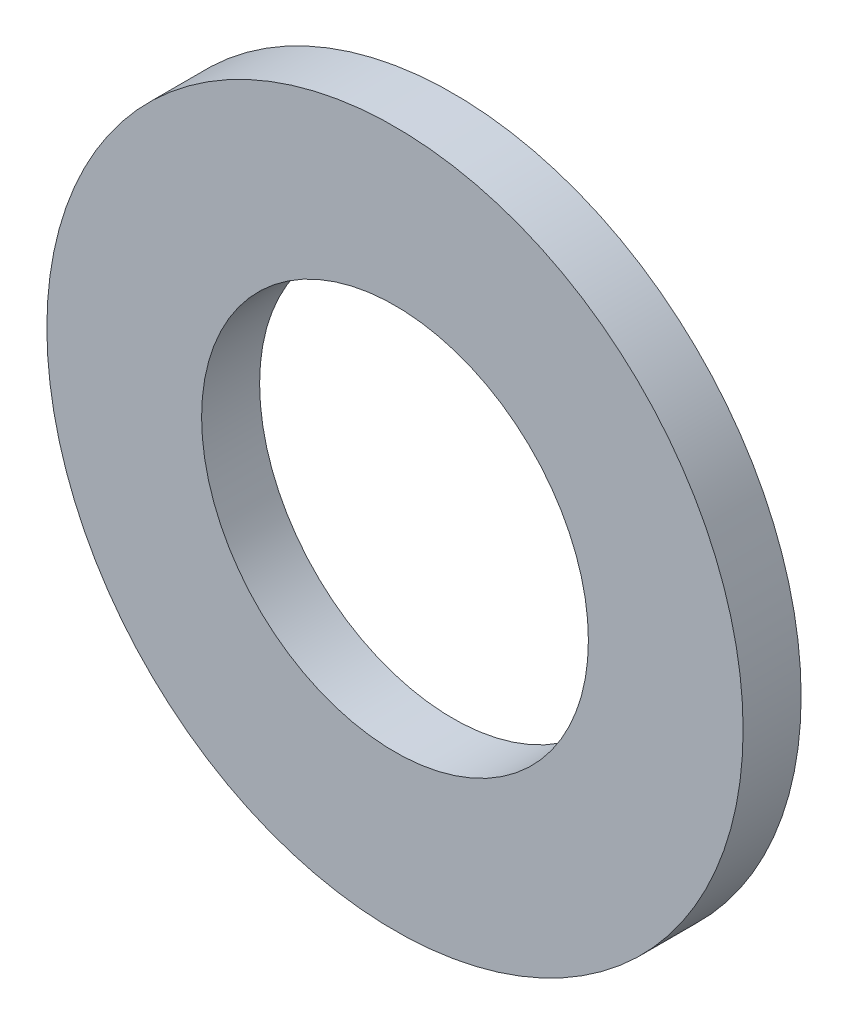
SolidWorks part; units mm, degrees
material "Commercial Bronze, UNS C22000 (90-10 Bronze)"
ref_plane "Front Plane" through (0, 0, 0) normal (0, 0, 1) x (1, 0, 0)
ref_plane "Top Plane" through (0, 0, 0) normal (0, 1, 0) x (1, 0, 0)
ref_plane "Right Plane" through (0, 0, 0) normal (1, 0, 0) x (0, 0, -1)
sketch "Sketch1" plane through (0, 0, 0) normal (0, 0, 1) x (1, 0, 0)
  circle A0 centre (0, 0) radius 9 construction
  circle A1 centre (0, 0) radius 5 construction
  dimension "OD" = 18
  dimension "ID" = 10
sketch "Sketch2" plane through (0, 0, 0) normal (1, 0, 0) x (0, 0, -1)
  line L2 (-0.75, 0) -> (0.75, 0) construction
  line L4 (-0.75, 9) -> (0.75, 9) construction
  line L6 (-0.75, 9) -> (-0.75, 0) construction
  line L9 (0.75, 9) -> (0.75, 0) construction
  line L10 (0, 9) -> (0, -9) construction
  point P0 (0, 9)
  point P6 (0, 0)
  dimension "T" = 1.5
sketch "Sketch5" plane through (0, 0, 0) normal (0, 0, 1) x (1, 0, 0)
  circle A0 centre (0, 0) radius 9
  circle A1 centre (0, 0) radius 5
  circle A2 centre (0, 0) radius 5 construction
  circle A3 centre (0, 0) radius 9 construction
extrude "Boss-Extrude1" add sketch "Sketch5" against normal up to vertex (0.75 mm away) and the other way up to vertex (0.75 mm away) up to point (0, 0, -0.75) other way up to point (0, 0, 0.75)
sketch "Sketch4" plane through (0, 0, 0) normal (0, 0, 1) x (1, 0, 0)
  line L0 (0, 0) -> (-3.5355, 3.5355) construction
  line L1 (0, -2.2) -> (0, 2.2) construction
  circle A1 centre (0, 0) radius 5 construction
  dimension "D1" = 45
